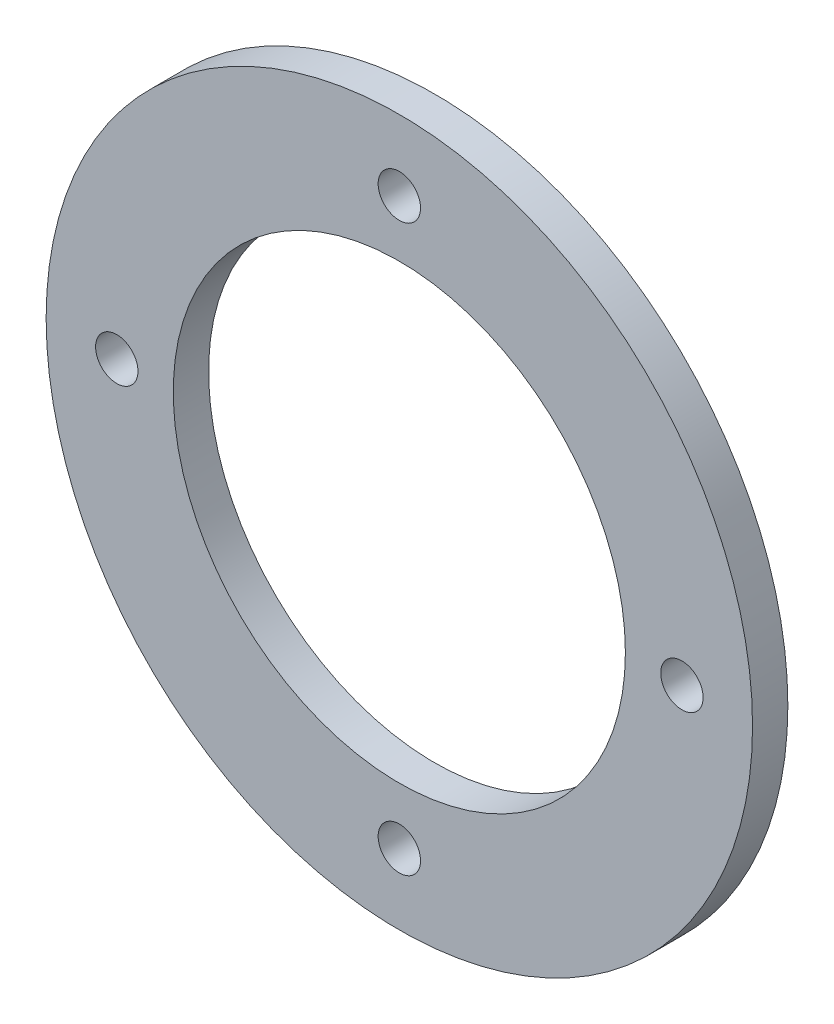
SolidWorks part; units mm, degrees
ref_plane "Płaszczyzna przednia" through (0, 0, 0) normal (0, 0, 1) x (1, 0, 0)
ref_plane "Płaszczyzna górna" through (0, 0, 0) normal (0, 1, 0) x (1, 0, 0)
ref_plane "Płaszczyzna prawa" through (0, 0, 0) normal (1, 0, 0) x (0, 0, -1)
sketch "Szkic1" plane through (0, 0, 0) normal (0, 0, 1) x (1, 0, 0)
  circle A0 centre (0, 0) radius 50
  dimension "D1" = 100
extrude "Dodanie-wyciągnięcie1" add sketch "Szkic1" along normal blind 5
sketch "Szkic2" plane through (0, 0, 5) normal (0, 0, 1) x (1, 0, 0)
  circle A0 centre (0, 0) radius 32
  dimension "D1" = 64
extrude "Wytnij-wyciągnięcie1" cut sketch "Szkic2" against normal blind 5
sketch "Szkic3" plane through (0, 0, 5) normal (0, 0, 1) x (1, 0, 0)
  circle A0 centre (0, 40) radius 3
  circle A1 centre (40, 0) radius 3
  circle A2 centre (0, -40) radius 3
  circle A3 centre (-40, 0) radius 3
  dimension "D1" = 6
  dimension "D2" = 40
  dimension "D3" = 4
extrude "Wytnij-wyciągnięcie2" cut sketch "Szkic3" against normal blind 5
